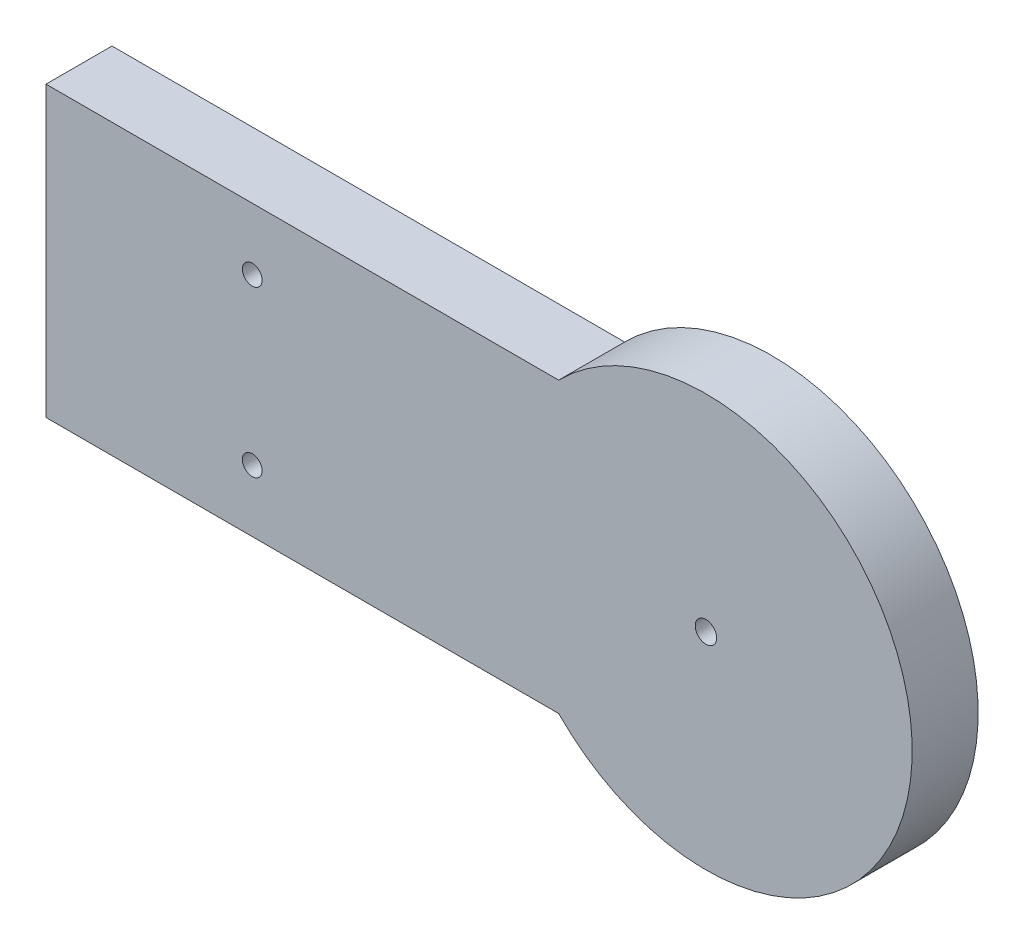
SolidWorks part; units mm, degrees
material "PLA"
ref_plane "Płaszczyzna przednia" through (0, 0, 0) normal (0, 0, 1) x (1, 0, 0)
ref_plane "Płaszczyzna górna" through (0, 0, 0) normal (0, 1, 0) x (1, 0, 0)
ref_plane "Płaszczyzna prawa" through (0, 0, 0) normal (1, 0, 0) x (0, 0, -1)
sketch "Szkic1" plane through (0, 0, 0) normal (0, 0, 1) x (1, 0, 0)
  line L0 (17.8536, 17.5) -> (182.1464, 17.5)
  line L1 (17.8536, -17.5) -> (182.1464, -17.5)
  arc A0 (17.8536, 17.5) -> (17.8536, -17.5) centre (0, 0) ccw
  arc A1 (182.1464, -17.5) -> (182.1464, 17.5) centre (200, 0) ccw
  dimension "D1" = 50
  dimension "D3" = 50
  dimension "D2" = 200
  dimension "D4" = 35
  dimension "D5" = 17.5
extrude "Dodanie-wyciągnięcie1" add sketch "Szkic1" along normal blind 8
sketch "Szkic2" plane through (0, 0, 8) normal (0, 0, 1) x (1, 0, 0)
  point P0 (-7.1, 0)
  point P1 (7.1, 0)
  dimension "D1" = 14.2
  dimension "D2" = 7.1
hole_wizard "Otwór pod śrubę M22" positions "Szkic11" profile "Szkic12" hole size "M2" standard "ISO" end condition up to next
sketch "Szkic11" plane through (0, 0, 8) normal (0, 0, -1) x (-1, 0, 0)
  arc A0 (-182.1464, 17.5) -> (-182.1464, -17.5) centre (-200, 0) ccw construction
  point P0 (-200, 0)
sketch "Szkic12" plane through (200, 0, 8) normal (1, 0, 0) x (0, -1, 0)
  line L0 (0, 0) -> (0, 8)
  line L1 (0, 8) -> (1.3, 8)
  line L2 (1.3, 8) -> (1.3, 0)
  line L5 (1.3, 0) -> (0, 0)
  line L11 (0, -6.35) -> (0, 107.95) construction
  dimension "Średnica otworu na wylot" = 2.6
  dimension "Głębokość otworu na wylot" = 8
shell "Skorupa1" thickness 3
sketch "Szkic15" plane through (0, 0, 0) normal (0, 0, -1) x (-1, 0, 0)
  line L0 (-16.5454, -14.5) -> (-183.4546, -14.5) construction
  line L1 (-183.4546, 14.5) -> (-16.5454, 14.5) construction
  line L2 (-16.5454, -14.5) -> (-19.1246, -14.5)
  line L3 (-16.5454, 14.5) -> (-19.1246, 14.5)
  line L4 (-180.8754, -14.5) -> (-183.4546, -14.5)
  line L5 (-180.8754, 14.5) -> (-183.4546, 14.5)
  arc A0 (-16.5454, -14.5) -> (-16.5454, 14.5) centre (0, 0) cw
  arc A1 (-16.5454, -14.5) -> (-16.5454, 14.5) centre (0, 0) ccw construction
  arc A2 (-19.1246, -14.5) -> (-19.1246, 14.5) centre (0, 0) cw
  arc A3 (-183.4546, -14.5) -> (-183.4546, 14.5) centre (-200, 0) ccw
  arc A4 (-183.4546, 14.5) -> (-183.4546, -14.5) centre (-200, 0) ccw construction
  arc A5 (-180.8754, -14.5) -> (-180.8754, 14.5) centre (-200, 0) ccw
  dimension "D1" = 2
  dimension "D2" = 22
  dimension "D3" = 24
  dimension "D4" = 2
extrude "Dodanie-wyciągnięcie2" add sketch "Szkic15" against normal up to next
hole_wizard "Otwór pod śrubę M21" positions "Szkic3" profile "Szkic4" hole size "M2" standard "ISO" end condition up to next
sketch "Szkic3" plane through (0, 0, 8) normal (0, 0, 1) x (1, 0, 0)
  point P0 (7.1, 0)
  point P3 (-7.1, 0)
sketch "Szkic4" plane through (7.1, 0, 8) normal (1, 0, 0) x (0, -1, 0)
  line L0 (0, 0) -> (0, 3)
  line L1 (0, 3) -> (1.3, 3)
  line L2 (1.3, 3) -> (1.3, 0)
  line L5 (1.3, 0) -> (0, 0)
  line L11 (0, -6.35) -> (0, 107.95) construction
  dimension "Średnica otworu na wylot" = 2.6
  dimension "Głębokość otworu na wylot" = 3
sketch "Szkic7" plane through (0, 0, 0) normal (0, 0, -1) x (-1, 0, 0)
  line L1 (-34.5, -10.5) -> (-75.5, -10.5)
  line L2 (-34.5, -10.5) -> (-34.5, 10.5)
  line L3 (-34.5, 10.5) -> (-75.5, 10.5)
  line L4 (-75.5, -10.5) -> (-75.5, 10.5)
  line L5 (-34.5, -10.5) -> (-75.5, 10.5) construction
  line L6 (-34.5, 10.5) -> (-75.5, -10.5) construction
  point P0 (-55, 0)
  dimension "D1" = 21
  dimension "D2" = 41
  dimension "D3" = 55
extrude "Wytnij-wyciągnięcie1" cut sketch "Szkic7" against normal up to next
hole_wizard "Otwory ustalające Ø8.0mm1" positions "Szkic5" profile "Szkic6" hole size "Ø8.0" standard "ISO" end condition up to next
sketch "Szkic5" plane through (0, 0, 8) normal (0, 0, -1) x (-1, 0, 0)
  point P0 (0, 0)
sketch "Szkic6" plane through (0, 0, 8) normal (1, 0, 0) x (0, -1, 0)
  line L0 (0, 0) -> (0, 3)
  line L1 (0, 3) -> (4, 3)
  line L2 (4, 3) -> (4, 0)
  line L5 (4, 0) -> (0, 0)
  line L11 (0, -6.35) -> (0, 107.95) construction
  dimension "Średnica otworu na wylot" = 8
  dimension "Głębokość otworu na wylot" = 3
ref_plane "Płaszczyzna2" through (50, 0, 0) normal (1, 0, 0) x (0, 0, -1)
sketch "Szkic18" plane through (50, 0, 0) normal (1, 0, 0) x (0, 0, -1)
  line L0 (0, -22) -> (0, 22) construction
  line L1 (-8, 23.5) -> (0, 23.5)
  line L2 (-8, 23.5) -> (-8, 17.5)
  line L3 (-8, 17.5) -> (0, 17.5)
  line L4 (0, 23.5) -> (0, 17.5)
  line L5 (-8, 23.5) -> (0, 17.5) construction
  line L6 (-8, 17.5) -> (0, 23.5) construction
  line L7 (-8, 25) -> (-8, -25) construction
  line L8 (-8, 17.5) -> (0, 17.5) construction
  line L9 (-7, 22.5) -> (-1, 22.5)
  line L10 (-1, 22.5) -> (-1, 18.5)
  line L11 (-7, 18.5) -> (-1, 18.5)
  line L12 (-7, 22.5) -> (-7, 18.5)
  point P0 (-4, 20.5)
  dimension "D1" = 6
  dimension "D2" = 1
extrude "Dodanie-wyciągnięcie3" add sketch "Szkic18" along normal blind 10
pattern_linear "Szyk liniowy1" count 2 spacing 50 along (1, 0, 0) of "Dodanie-wyciągnięcie3"
sketch "Szkic19" plane through (0, 0, 5) normal (0, 0, -1) x (-1, 0, 0)
  line L0 (-100, 17.5) -> (-60, 17.5) construction
  line L1 (-95, -10) -> (-145, -10)
  line L2 (-95, -10) -> (-95, 10)
  line L3 (-95, 10) -> (-145, 10)
  line L4 (-145, -10) -> (-145, 10)
  line L5 (-95, -10) -> (-145, 10) construction
  line L6 (-95, 10) -> (-145, -10) construction
  circle A0 centre (0, 0) radius 4 construction
  point P0 (-120, 0)
  dimension "D1" = 50
  dimension "D2" = 20
  dimension "D3" = 120
  dimension "D4" = 17.5
  dimension "D5" = 2.2
ref_plane "Płaszczyzna3" through (120, 0, 0) normal (1, 0, 0) x (0, 0, -1)
hole_wizard "Otwór pod śrubę M24" positions "Szkic22" profile "Szkic21" hole size "M2" standard "ISO" end condition through all
sketch "Szkic22" plane through (0, 0, 5) normal (0, 0, -1) x (-1, 0, 0)
  point P0 (-145, -10)
  point P3 (-145, 10)
  point P6 (-95, 10)
  point P9 (-95, -10)
sketch "Szkic21" plane through (145, -10, 5) normal (1, 0, 0) x (0, 1, 0)
  line L0 (0, 0) -> (0, 3)
  line L1 (0, 3) -> (1.2, 3)
  line L2 (1.2, 3) -> (1.2, 0)
  line L5 (1.2, 0) -> (0, 0)
  line L11 (0, -6.35) -> (0, 107.95) construction
  dimension " rednica otworu na wylot" = 2.4
  dimension "G³êboko æ otworu na wylot" = 3
other "Cięcie powierzchnią1"
ref_plane "Blat stołu" through (0, 0, 8) normal (0, 0, 1) x (1, 0, 0)
